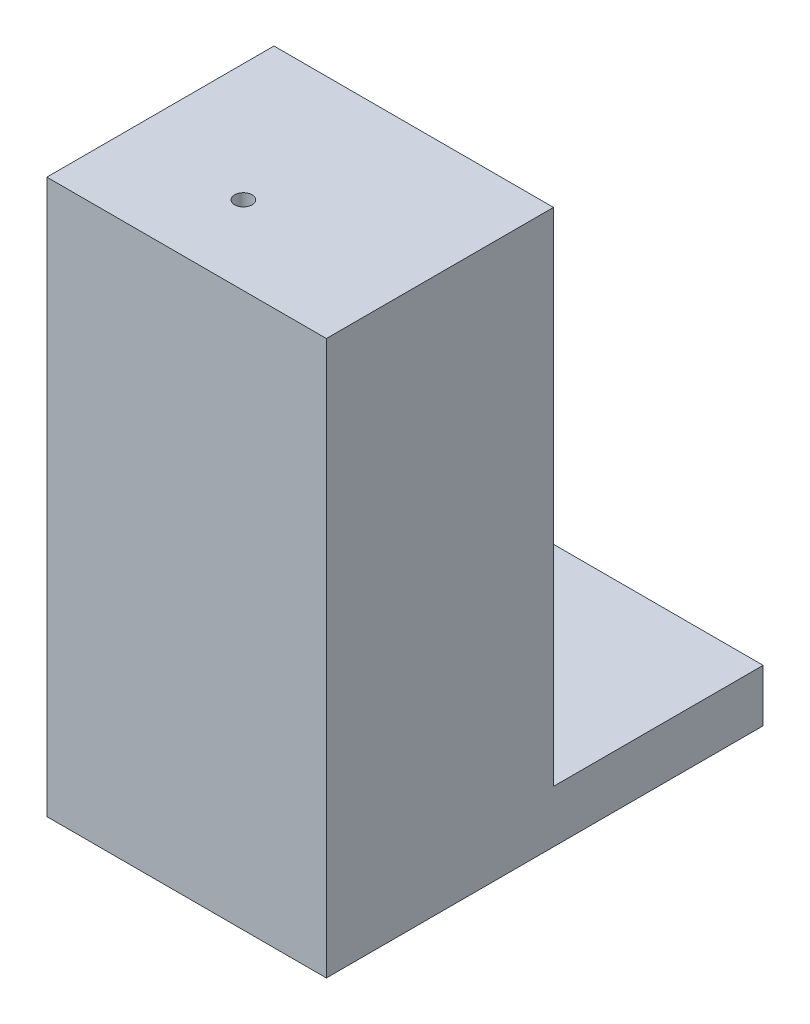
SolidWorks part; units mm, degrees
ref_plane "Front Plane" through (0, 0, 0) normal (0, 0, 1) x (1, 0, 0)
ref_plane "Top Plane" through (0, 0, 0) normal (0, 1, 0) x (1, 0, 0)
ref_plane "Right Plane" through (0, 0, 0) normal (1, 0, 0) x (0, 0, -1)
sketch "Sketch1" plane through (0, 0, 0) normal (1, 0, 0) x (0, 0, -1)
  line L0 (25, 0) -> (0, 0)
  line L1 (0, 0) -> (0, 31.7)
  line L2 (0, 31.7) -> (5.035, 31.7)
  line L3 (3, 21.7) -> (3, 16.7)
  line L4 (3, 16.7) -> (5.4, 16.7)
  line L5 (5.4, 16.7) -> (5.4, 13)
  line L6 (5.4, 13) -> (3, 13)
  line L7 (3, 13) -> (3, 3)
  line L8 (3, 3) -> (25, 3)
  line L9 (25, 3) -> (25, 0)
  line L10 (5.035, 31.7) -> (13, 31.7)
  line L11 (13, 31.7) -> (13, 21.7)
  line L12 (13, 21.7) -> (3, 21.7)
  dimension "D1" = 3.7
  dimension "D2" = 10
  dimension "D3" = 3
  dimension "D4" = 10
  dimension "D5" = 3
  dimension "D6" = 2.4
  dimension "D7" = 25
  dimension "D8" = 13
  dimension "D9" = 5
extrude "Boss-Extrude1" add sketch "Sketch1" along normal blind 16
sketch "Sketch2" plane through (16, 0, 0) normal (1, 0, 0) x (0, 0, -1)
  line L0 (25, 3) -> (3, 3) construction
  line L1 (3, 21.7) -> (13, 21.7)
  line L2 (3, 21.7) -> (3, 3)
  line L3 (3, 3) -> (13, 3)
  line L4 (13, 21.7) -> (13, 3)
  point P4 (13, 21.8)
  point P5 (13, 3)
extrude "Boss-Extrude2" add sketch "Sketch2" against normal blind 3
sketch "Sketch3" plane through (0, 31.7, 0) normal (0, 1, 0) x (1, 0, 0)
  line L0 (13, 13) -> (13, 3) construction
  line L1 (13, 3) -> (0, 3) construction
  circle A0 centre (6.75, 4.5) radius 0.5
  point P2 (0, 0)
  dimension "D1" = 1
  dimension "D2" = 6.25
  dimension "D3" = 1.5
extrude "Cut-Extrude1" cut sketch "Sketch3" against normal up to next
